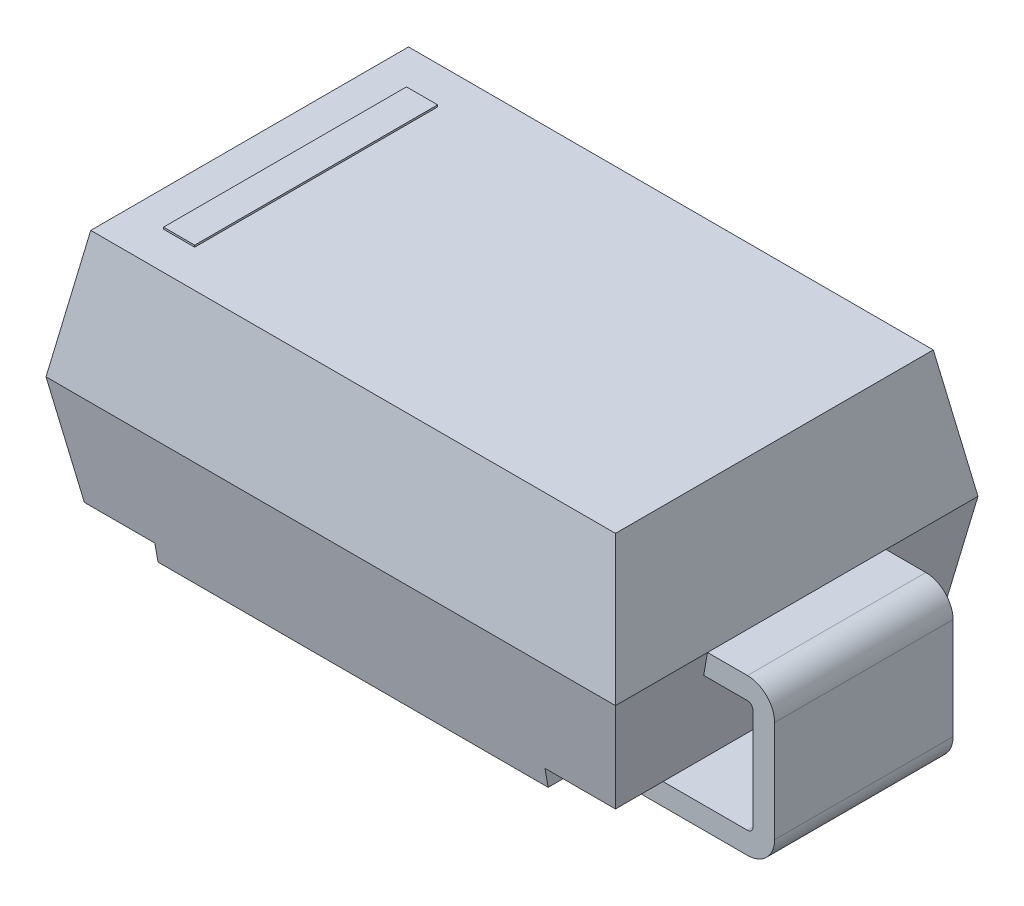
SolidWorks part; units mm, degrees
ref_plane "Front Plane" through (0, 0, 0) normal (0, 0, 1) x (1, 0, 0)
ref_plane "Top Plane" through (0, 0, 0) normal (0, 1, 0) x (1, 0, 0)
ref_plane "Right Plane" through (0, 0, 0) normal (1, 0, 0) x (0, 0, -1)
sketch "Sketch1" plane through (0, 0, 0) normal (0, 1, 0) x (1, 0, 0)
  line L1 (1.995, -1.27) -> (-1.995, -1.27)
  line L2 (1.995, -1.27) -> (1.995, 1.27)
  line L3 (1.995, 1.27) -> (-1.995, 1.27)
  line L4 (-1.995, -1.27) -> (-1.995, 1.27)
  line L5 (1.995, -1.27) -> (-1.995, 1.27) construction
  line L6 (1.995, 1.27) -> (-1.995, -1.27) construction
  point P0 (0, 0)
  dimension "D1" = 3.99
  dimension "D2" = 2.54
extrude "Boss-Extrude1" add sketch "Sketch1" along normal mid plane 1.777 draft 10
sketch "Sketch2" plane through (0, 0, 0) normal (0, 0, 1) x (1, 0, 0)
  line L0 (-1.995, 0) -> (-2.2745, 0)
  line L1 (-2.465, -0.1905) -> (-2.465, -0.901)
  line L2 (-2.2745, -1.0915) -> (-1.4183, -1.0915)
  line L3 (-1.8383, 0.8885) -> (1.8383, 0.8885) construction
  line L4 (0, 0) -> (0, 1.9534) construction
  line L5 (2.2745, -1.0915) -> (1.4183, -1.0915)
  line L6 (2.465, -0.1905) -> (2.465, -0.901)
  line L7 (1.995, 0) -> (2.2745, 0)
  line L8 (-1.9681, -0.1524) -> (-2.2745, -0.1524)
  line L9 (-2.3126, -0.1905) -> (-2.3126, -0.901)
  line L10 (-2.2745, -0.9391) -> (-1.4183, -0.9391)
  line L11 (-1.995, -0.1524) -> (-2.2745, -0.1524) construction
  line L12 (-1.8383, -0.8885) -> (-1.995, 0) construction
  line L13 (-1.4183, -0.9391) -> (-1.4183, -1.0915)
  line L14 (-1.9681, -0.1524) -> (-1.995, 0)
  line L15 (1.9681, -0.1524) -> (2.2745, -0.1524)
  line L16 (2.3126, -0.1905) -> (2.3126, -0.901)
  line L17 (2.2745, -0.9391) -> (1.4183, -0.9391)
  line L18 (1.995, -0.1524) -> (2.2745, -0.1524) construction
  line L19 (1.8383, -0.8885) -> (1.995, 0) construction
  line L20 (1.4183, -1.0915) -> (1.4183, -0.9391)
  line L21 (1.9681, -0.1524) -> (1.995, 0)
  arc A0 (2.465, -0.1905) -> (2.2745, 0) centre (2.2745, -0.1905) ccw
  arc A1 (-2.2745, 0) -> (-2.465, -0.1905) centre (-2.2745, -0.1905) ccw
  arc A2 (2.2745, -1.0915) -> (2.465, -0.901) centre (2.2745, -0.901) ccw
  arc A3 (-2.465, -0.901) -> (-2.2745, -1.0915) centre (-2.2745, -0.901) ccw
  arc A4 (-2.2745, -0.1524) -> (-2.3126, -0.1905) centre (-2.2745, -0.1905) ccw
  arc A5 (-2.3126, -0.901) -> (-2.2745, -0.9391) centre (-2.2745, -0.901) ccw
  arc A6 (2.3126, -0.1905) -> (2.2745, -0.1524) centre (2.2745, -0.1905) ccw
  arc A7 (2.2745, -0.9391) -> (2.3126, -0.901) centre (2.2745, -0.901) ccw
  point P16 (2.465, 0)
  point P19 (-2.465, 0)
  point P22 (2.465, -1.0915)
  point P25 (-2.465, -1.0915)
  dimension "D4" = 0.1905
  dimension "D1" = 1.98
  dimension "D2" = 0.1524
  dimension "D3" = 4.93
  dimension "D5" = 0.8562
  dimension "D6" = 0.1524
extrude "Boss-Extrude2" add sketch "Sketch2" along normal mid plane 1.25
sketch "Sketch3" plane through (0, 0, 0) normal (0, 0, 1) x (1, 0, 0)
  line L0 (-1.8383, -0.8885) -> (1.8383, -0.8885) construction
  line L1 (-1.8383, -0.8885) -> (-1.3667, -0.8885)
  line L2 (-1.8607, -0.7617) -> (-1.3667, -0.7617)
  line L3 (-1.8383, -0.8885) -> (-1.995, 0) construction
  line L4 (1.8383, -0.8885) -> (1.995, 0) construction
  line L5 (0, 0) -> (0, -1.8692) construction
  line L8 (-1.8383, -0.8885) -> (-1.8607, -0.7617)
  line L9 (1.8383, -0.8885) -> (1.8607, -0.7617)
  line L10 (-1.3667, -0.7617) -> (-1.3667, -0.8885)
  line L11 (1.3667, -0.7617) -> (1.3667, -0.8885)
  line L12 (1.3667, -0.7617) -> (1.8607, -0.7617)
  line L13 (1.3667, -0.8885) -> (1.8383, -0.8885)
extrude "Cut-Extrude1" cut sketch "Sketch3" against normal up to next and the other way up to next
sketch "Sketch5" plane through (0, 0.8885, 0) normal (0, 1, 0) x (1, 0, 0)
  line L0 (0, 0) -> (-1.7923, 0) construction
  line L1 (-1.5904, 0.8511) -> (-1.3722, 0.8511)
  line L2 (-1.5904, 0.8511) -> (-1.5904, -0.8511)
  line L3 (-1.5904, -0.8511) -> (-1.3722, -0.8511)
  line L4 (-1.3722, 0.8511) -> (-1.3722, -0.8511)
extrude "Boss-Extrude3" add sketch "Sketch5" along normal blind 0.0127
